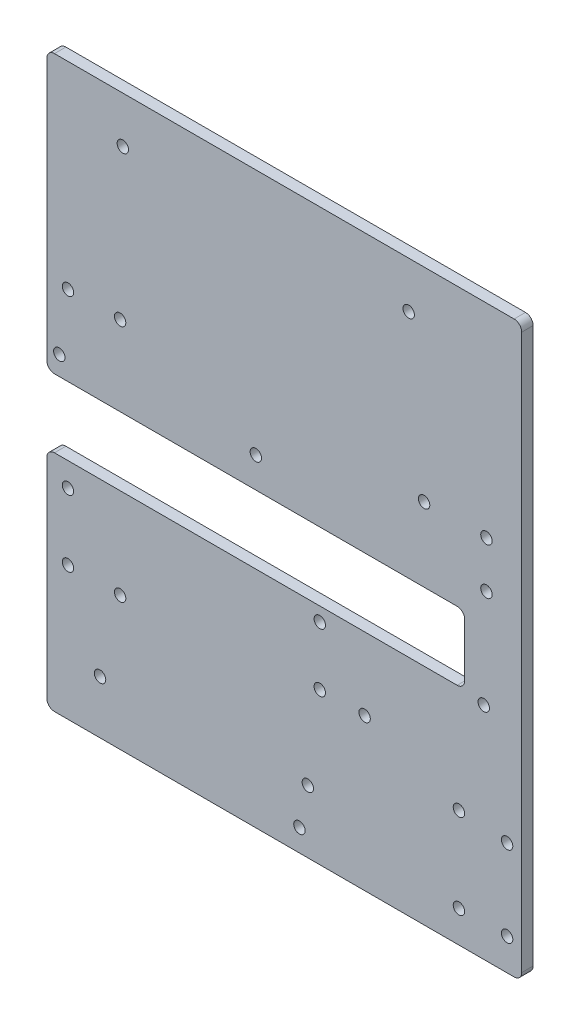
SolidWorks part; units mm, degrees
ref_plane "前视基准面" through (0, 0, 0) normal (0, 0, 1) x (1, 0, 0)
ref_plane "上视基准面" through (0, 0, 0) normal (0, 1, 0) x (1, 0, 0)
ref_plane "右视基准面" through (0, 0, 0) normal (1, 0, 0) x (0, 0, -1)
sketch "草图1" plane through (0, 0, 0) normal (0, 0, 1) x (1, 0, 0)
  line L0 (-42.6461, 31.1124) -> (-42.6461, 7.1124) construction
  line L1 (-42.6461, 31.1124) -> (82.3539, 31.1124)
  line L2 (-42.6461, 31.1124) -> (-42.6461, -68.8876)
  line L3 (-42.6461, -68.8876) -> (82.3539, -68.8876)
  line L4 (82.3539, 31.1124) -> (82.3539, -68.8876)
  circle A0 centre (-37.0961, 29.1324) radius 1.5
  circle A1 centre (-23.3661, 29.1324) radius 1.5
  circle A2 centre (-39.3761, 13.1824) radius 1.5
  circle A3 centre (-37.0961, -16.1976) radius 1.5
  circle A4 centre (-37.0961, -33.7076) radius 1.5
  circle A5 centre (-23.3661, -33.7076) radius 1.5
  circle A6 centre (56.6539, 27.5724) radius 1.5
  circle A7 centre (73.0639, 27.5724) radius 1.5
  circle A8 centre (73.0639, 15.3624) radius 1.5
  circle A9 centre (29.1939, -13.5576) radius 1.5
  circle A10 centre (29.1939, -28.9676) radius 1.5
  circle A11 centre (40.9939, -28.9676) radius 1.5
  circle A12 centre (26.0439, -52.3676) radius 1.5
  circle A13 centre (23.8339, -63.0576) radius 1.5
  circle A14 centre (65.8239, -60.5176) radius 1.5
  circle A15 centre (78.5039, -60.5176) radius 1.5
  circle A16 centre (78.5039, -39.2676) radius 1.5
  circle A18 centre (65.8239, -38.1776) radius 1.5
  circle A19 centre (-28.6461, -54.8876) radius 1.5
  circle A20 centre (72.3539, -10.8876) radius 1.5
  circle A22 centre (12.3539, 16.1124) radius 1.5
  dimension "D4" = 3
  dimension "D7" = 3
  dimension "D8" = 3
  dimension "D13" = 3
  dimension "D15" = 3
  dimension "D17" = 3
  dimension "D20" = 3
  dimension "D22" = 3
  dimension "D23" = 3
  dimension "D24" = 12.21
  dimension "D27" = 3
  dimension "D29" = 3
  dimension "D31" = 3
  dimension "D34" = 3
  dimension "D35" = 3
  dimension "D40" = 3
  dimension "D42" = 3
  dimension "D43" = 3
  dimension "D45" = 3
  dimension "D47" = 14
  dimension "D48" = 14
  dimension "D49" = 3
  dimension "D50" = 3
  dimension "D51" = 10
  dimension "D52" = 58
  dimension "D53" = 3
  dimension "D54" = 85
  dimension "D55" = 70
  dimension "D1" = 125
  dimension "D2" = 100
  dimension "D3" = 5.55
  dimension "D5" = 1.98
  dimension "D6" = 13.73
  dimension "D9" = 15.95
  dimension "D10" = 2.28
  dimension "D11" = 29.38
  dimension "D12" = 2.28
  dimension "D14" = 17.51
  dimension "D16" = 13.73
  dimension "D18" = 80.02
  dimension "D19" = 1.56
  dimension "D21" = 16.41
  dimension "D25" = 66.29
  dimension "D26" = 2.64
  dimension "D28" = 15.41
  dimension "D30" = 11.8
  dimension "D32" = 23.4
  dimension "D33" = 3.15
  dimension "D36" = 10.69
  dimension "D37" = 2.21
  dimension "D38" = 41.99
  dimension "D39" = 2.54
  dimension "D41" = 12.68
  dimension "D44" = 21.25
  dimension "D46" = 22.34
extrude "凸台-拉伸1" add sketch "草图1" along normal blind 3
sketch "草图2" plane through (0, 0, 0) normal (0, 0, -1) x (-1, 0, 0)
  line L0 (42.6461, -9.8876) -> (-67.3539, -9.8876)
  line L1 (42.6461, 31.1124) -> (42.6461, -68.8876) construction
  line L2 (-67.3539, -9.8876) -> (-67.3539, 8.1124)
  line L3 (-67.3539, 8.1124) -> (42.6461, 8.1124)
  line L4 (42.6461, 8.1124) -> (42.6461, -9.8876)
  line L5 (-82.3539, 31.1124) -> (42.6461, 31.1124) construction
  dimension "D1" = 23
  dimension "D2" = 18
  dimension "D3" = 110
extrude "切除-拉伸1" cut sketch "草图2" against normal through all
sketch "草图3" plane through (0, 31.1124, 0) normal (0, 1, 0) x (1, 0, 0)
  line L0 (-42.6461, 0) -> (-42.6461, -3)
  line L1 (-42.6461, -3) -> (82.3539, -3)
  line L2 (82.3539, -3) -> (82.3539, 0)
  line L3 (82.3539, 0) -> (-42.6461, 0)
extrude "凸台-拉伸2" add sketch "草图3" along normal blind 50
sketch "草图4" plane through (0, 0, 0) normal (0, 0, -1) x (-1, 0, 0)
  line L0 (-82.3539, -68.8876) -> (-82.3539, 81.1124) construction
  line L1 (-82.3539, 81.1124) -> (42.6461, 81.1124) construction
  circle A0 centre (-52.6039, 68.9224) radius 1.5
  circle A1 centre (22.6561, 68.9224) radius 1.5
  dimension "D1" = 3
  dimension "D2" = 29.75
  dimension "D4" = 3
  dimension "D5" = 75.26
  dimension "D3" = 12.19
extrude "切除-拉伸2" cut sketch "草图4" against normal through all
fillet "圆角1" radius 2 8 edges at (67.3539, -9.8876, 1.5) (67.3539, 8.1124, 1.5) (-42.6461, 8.1124, 1.5) (-42.6461, -9.8876, 1.5) (-42.6461, -68.8876, 1.5) (82.3539, -68.8876, 1.5) (-42.6461, 81.1124, 1.5) (82.3539, 81.1124, 1.5)
